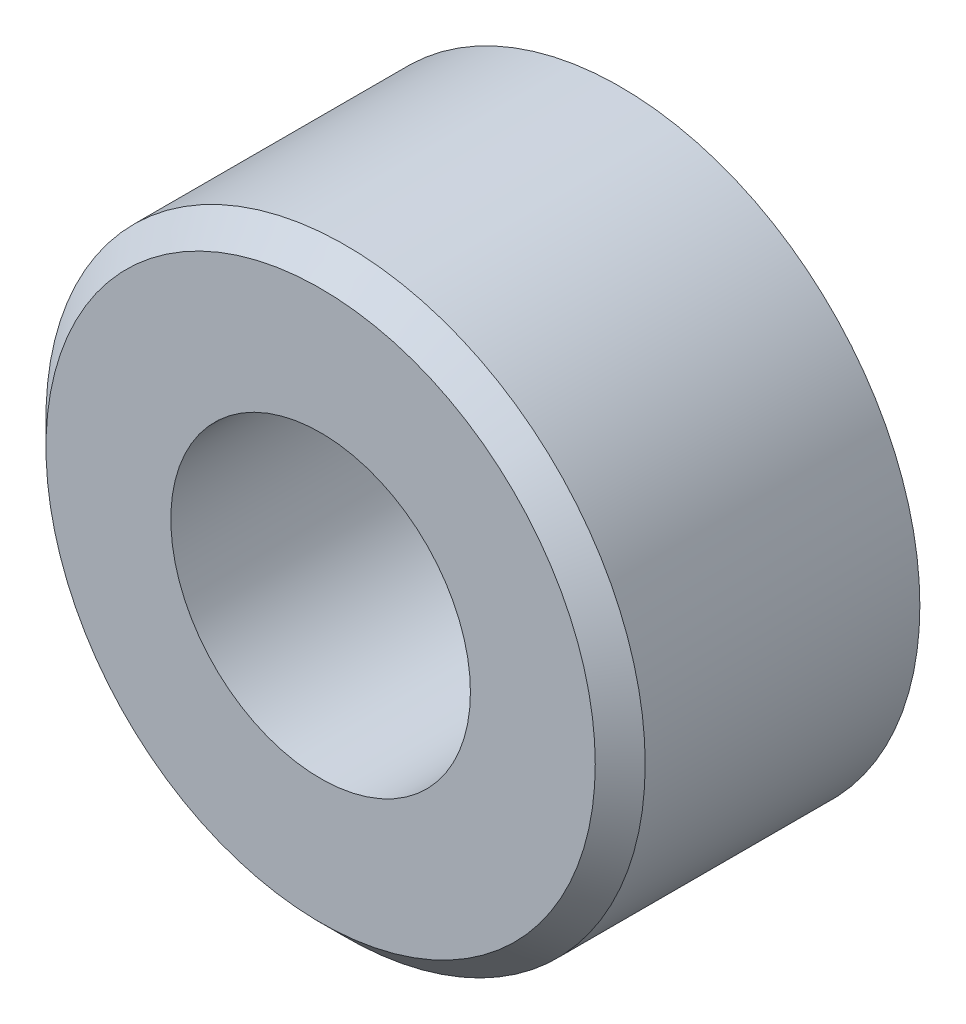
SolidWorks part; units mm, degrees
ref_plane "Front Plane" through (0, 0, 0) normal (0, 0, 1) x (1, 0, 0)
ref_plane "Top Plane" through (0, 0, 0) normal (0, 1, 0) x (1, 0, 0)
ref_plane "Right Plane" through (0, 0, 0) normal (1, 0, 0) x (0, 0, -1)
sketch "Sketch1" plane through (0, 0, 0) normal (0, 0, 1) x (1, 0, 0)
  circle A0 centre (0, 0) radius 6
  circle A1 centre (0, 0) radius 3
  dimension "D1" = 6
  dimension "D2" = 12
extrude "Boss-Extrude1" add sketch "Sketch1" along normal blind 6
chamfer "Chamfer1" distance 0.5 angle 45 1 edges at (6, 0, 6)
